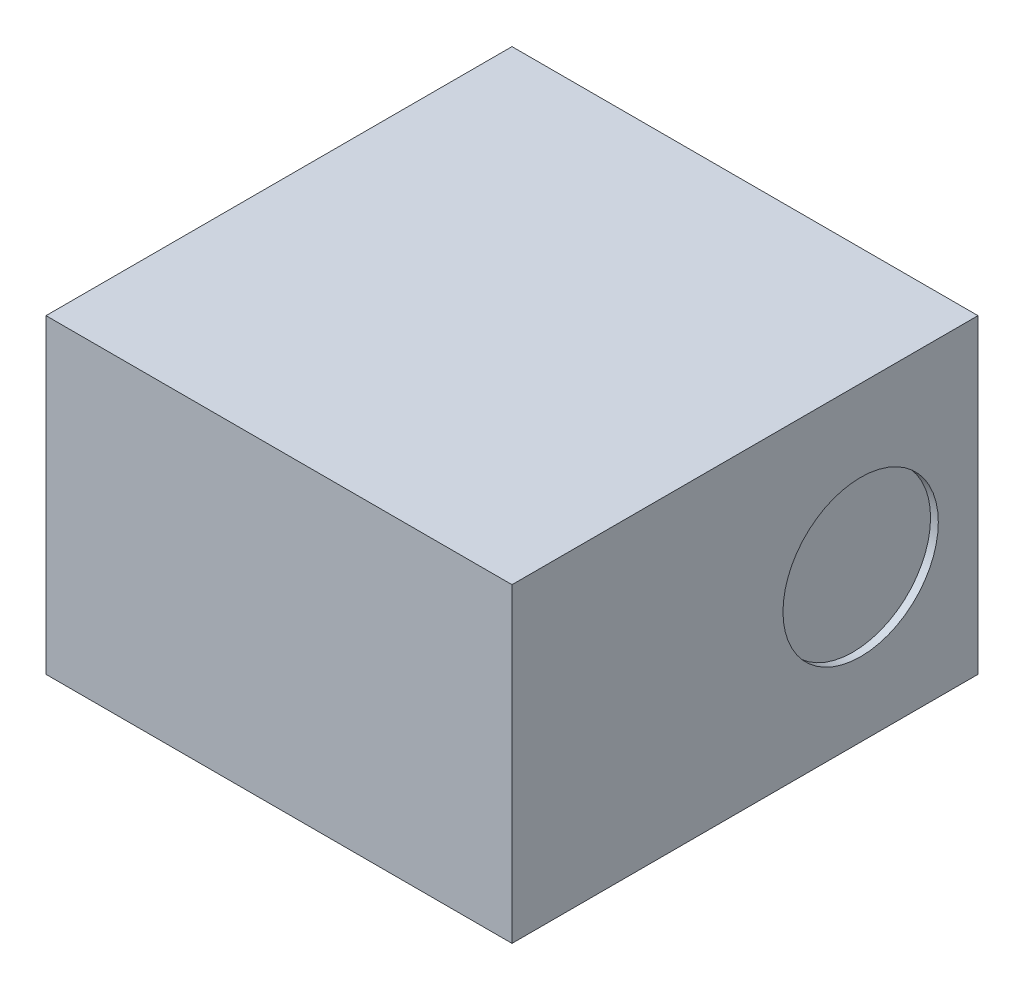
SolidWorks part; units mm, degrees
ref_plane "Front Plane" through (0, 0, 0) normal (0, 0, 1) x (1, 0, 0)
ref_plane "Top Plane" through (0, 0, 0) normal (0, 1, 0) x (1, 0, 0)
ref_plane "Right Plane" through (0, 0, 0) normal (1, 0, 0) x (0, 0, -1)
sketch "Sketch1" plane through (0, 0, 0) normal (0, 1, 0) x (1, 0, 0)
  line L0 (0, 0) -> (18.6879, 0) construction
  line L1 (0, 0) -> (0, -14.4281) construction
  line L3 (-1.5, 1.5) -> (1.5, 1.5)
  line L4 (-1.5, 1.5) -> (-1.5, -1.5)
  line L5 (-1.5, -1.5) -> (1.5, -1.5)
  line L6 (1.5, 1.5) -> (1.5, -1.5)
  dimension "D1" = 3
extrude "Boss-Extrude1" add sketch "Sketch1" along normal blind 2
sketch "Sketch2" plane through (1.5, 0, 0) normal (1, 0, 0) x (0, 0, -1)
  circle A1 centre (0.7445, 0.9763) radius 0.5
extrude "Cut-Extrude1" cut sketch "Sketch2" against normal blind 0.05
